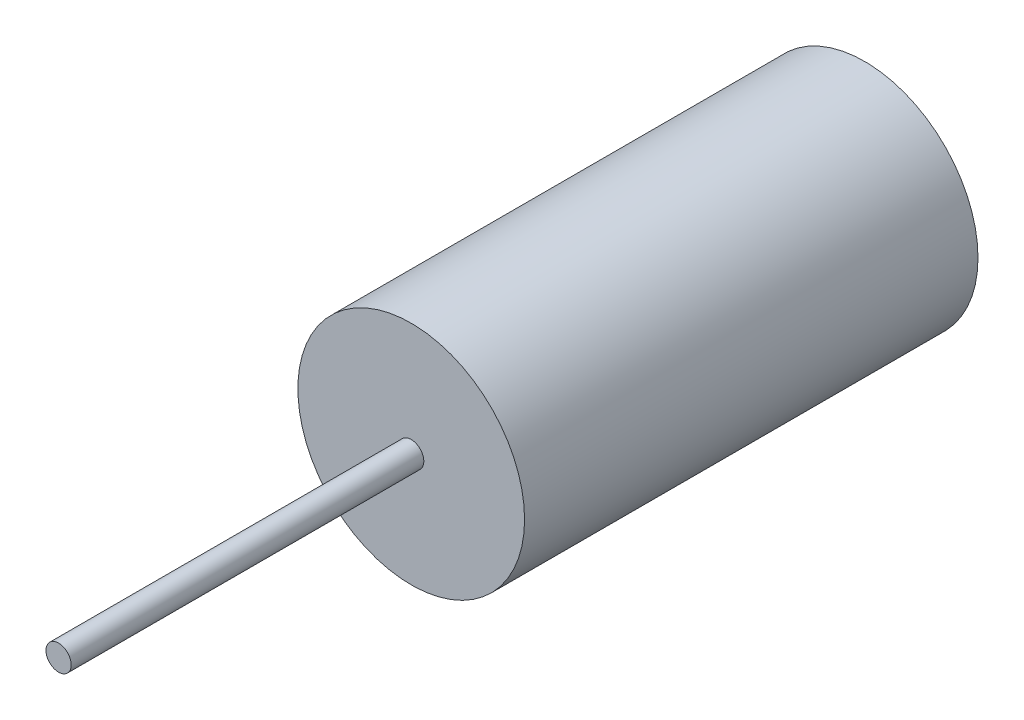
SolidWorks part; units mm, degrees
ref_plane "Front Plane" through (0, 0, 0) normal (0, 0, 1) x (1, 0, 0)
ref_plane "Top Plane" through (0, 0, 0) normal (0, 1, 0) x (1, 0, 0)
ref_plane "Right Plane" through (0, 0, 0) normal (1, 0, 0) x (0, 0, -1)
sketch "Sketch1" plane through (0, 0, 0) normal (0, 0, 1) x (1, 0, 0)
  circle A0 centre (0, 0) radius 57.15
  dimension "D1" = 114.3
extrude "Boss-Extrude1" add sketch "Sketch1" along normal blind 228.6
sketch "Sketch2" plane through (0, 0, 228.6) normal (0, 0, 1) x (1, 0, 0)
  circle A0 centre (0, 0) radius 6.35
  dimension "D1" = 12.7
extrude "Boss-Extrude2" add sketch "Sketch2" along normal blind 177.8
